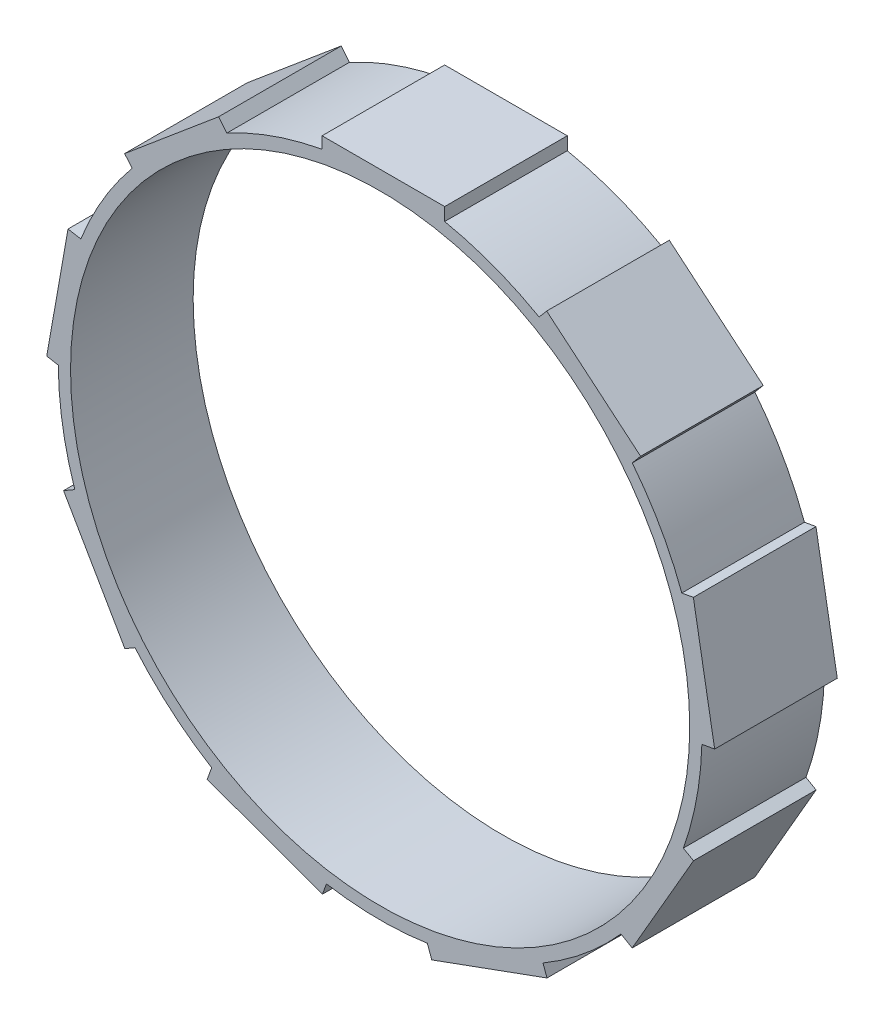
SolidWorks part; units mm, degrees
ref_plane "Alzado" through (0, 0, 0) normal (0, 0, 1) x (1, 0, 0)
ref_plane "Planta" through (0, 0, 0) normal (0, 1, 0) x (1, 0, 0)
ref_plane "Vista lateral" through (0, 0, 0) normal (1, 0, 0) x (0, 0, -1)
sketch "Croquis1" plane through (0, 0, 0) normal (0, 0, 1) x (1, 0, 0)
  line L0 (12.9676, 22.8233) -> (13.5817, 23.5551)
  line L2 (-4.7368, 25.8191) -> (-4.7368, 26.7744)
  line L3 (-4.7368, 26.7744) -> (5.2632, 26.7744)
  line L4 (5.2632, 25.7169) -> (5.2632, 26.7744)
  line L5 (-4.5088, 25.8008) -> (5.2632, 26.7744) construction
  line L6 (-4.7368, 26.7744) -> (5.9461, 25.5917) construction
  line L7 (13.5817, 23.5551) -> (21.2421, 17.1272)
  line L8 (20.5624, 16.3172) -> (21.2421, 17.1272)
  line L9 (24.6043, 9.1482) -> (25.5451, 9.3141)
  line L10 (25.5451, 9.3141) -> (27.2816, -0.534)
  line L11 (26.2402, -0.7176) -> (27.2816, -0.534)
  line L12 (24.7284, -8.8074) -> (25.5557, -9.2851)
  line L13 (25.5557, -9.2851) -> (20.5557, -17.9453)
  line L14 (19.6399, -17.4166) -> (20.5557, -17.9453)
  line L15 (13.2817, -22.6419) -> (13.6085, -23.5397)
  line L16 (13.6085, -23.5397) -> (4.2116, -26.9599)
  line L17 (3.8499, -25.9662) -> (4.2116, -26.9599)
  line L18 (-4.3796, -25.8821) -> (-4.7063, -26.7798)
  line L19 (-4.7063, -26.7798) -> (-14.1032, -23.3596)
  line L20 (-13.7415, -22.3659) -> (-14.1032, -23.3596)
  line L21 (-19.9916, -17.0117) -> (-20.819, -17.4894)
  line L22 (-20.819, -17.4894) -> (-25.819, -8.8291)
  line L23 (-24.9031, -8.3004) -> (-25.819, -8.8291)
  line L24 (-26.2494, -0.1814) -> (-27.1902, -0.0155)
  line L25 (-27.1902, -0.0155) -> (-25.4537, 9.8326)
  line L26 (-24.4123, 9.649) -> (-25.4537, 9.8326)
  line L27 (-20.2248, 16.7338) -> (-20.8388, 17.4657)
  line L28 (-20.8388, 17.4657) -> (-13.1784, 23.8935)
  line L29 (-12.4986, 23.0835) -> (-13.1784, 23.8935)
  circle A0 centre (0, 0) radius 25.25
  arc A1 (-4.7368, 25.8191) -> (-12.4986, 23.0835) centre (0, 0) ccw
  arc A2 (12.9676, 22.8233) -> (5.2632, 25.7169) centre (0, 0) ccw
  arc A3 (-20.2248, 16.7338) -> (-24.4123, 9.649) centre (0, 0) ccw
  arc A4 (-26.2494, -0.1814) -> (-24.9031, -8.3004) centre (0, 0) ccw
  arc A5 (-19.9916, -17.0117) -> (-13.7415, -22.3659) centre (0, 0) ccw
  arc A6 (-4.3796, -25.8821) -> (3.8499, -25.9662) centre (0, 0) ccw
  arc A7 (13.2817, -22.6419) -> (19.6399, -17.4166) centre (0, 0) ccw
  arc A8 (24.7284, -8.8074) -> (26.2402, -0.7176) centre (0, 0) ccw
  arc A9 (24.6043, 9.1482) -> (20.5624, 16.3172) centre (0, 0) ccw
  point P4 (0, 26.25)
  point P44 (0, 0)
  dimension "D1" = 50.5
  dimension "D2" = 1
  dimension "D4" = 1
  dimension "D5" = 10
  dimension "D3" = 9
extrude "Saliente-Extruir1" add sketch "Croquis1" along normal blind 10
